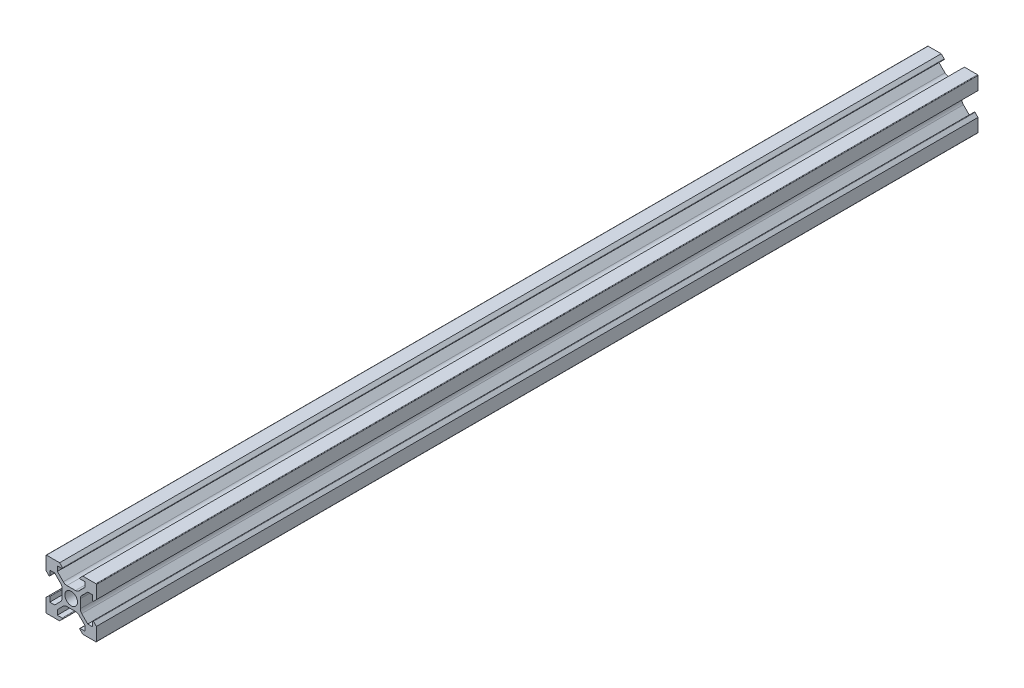
SolidWorks part; units mm, degrees
material "Liga 1350"
ref_plane "Plano frontal" through (0, 0, 0) normal (0, 0, 1) x (1, 0, 0)
ref_plane "Plano superior" through (0, 0, 0) normal (0, 1, 0) x (1, 0, 0)
ref_plane "Plano direito" through (0, 0, 0) normal (1, 0, 0) x (0, 0, -1)
sketch "Esboço1" plane through (0, 0, 0) normal (0, 0, 1) x (1, 0, 0)
  line L0 (0, 13.8681) -> (0, -15.879) construction
  line L1 (-4.6, -10) -> (-9.8, -10)
  line L2 (-3.4414, -8.8414) -> (-4.6, -10)
  line L3 (-4.1858, -3.1251) -> (-6.5607, -5.5)
  line L4 (-10, 9.8) -> (-10, 4.6)
  line L5 (-5.5, -8.5) -> (-3.5828, -8.5)
  line L6 (-5.5, -8.5) -> (-5.5, -6.5607)
  line L7 (-8.5, -5.5) -> (-8.5, -3.5828)
  line L8 (-21.5514, 0) -> (2.5, 0) construction
  line L9 (-3.1251, 4.1858) -> (-5.5, 6.5607)
  line L10 (-8.8414, -3.4414) -> (-10, -4.6)
  line L11 (-8.5, 5.5) -> (-6.5607, 5.5)
  line L12 (-8.8414, 3.4414) -> (-10, 4.6)
  line L13 (-8.5, -5.5) -> (-6.5607, -5.5)
  line L14 (-8.5, 5.5) -> (-8.5, 3.5828)
  line L15 (-3.1251, -4.1858) -> (-5.5, -6.5607)
  line L16 (-21.5514, 0) -> (20.6623, 0) construction
  line L17 (-8.5, 10) -> (-8.5, -10) construction
  line L18 (-10, -9.8) -> (-10, -4.6)
  line L19 (-21.5514, 5.5) -> (20.6623, 5.5) construction
  line L21 (-10, 10) -> (-10, -10) construction
  line L22 (3.6, 1.7109) -> (3.6, 0) construction
  line L23 (21.5514, 0) -> (-2.5, 0) construction
  line L24 (4.6, 10) -> (9.8, 10)
  line L25 (-5.5, 8.5) -> (-5.5, 6.5607)
  line L26 (3.4414, 8.8414) -> (4.6, 10)
  line L27 (-5.5, 8.5) -> (-3.5828, 8.5)
  line L28 (4.1858, 3.1251) -> (6.5607, 5.5)
  line L29 (5.5, 8.5) -> (3.5828, 8.5)
  line L30 (5.5, 8.5) -> (5.5, 6.5607)
  line L31 (-3.6, 1.7109) -> (-3.6, -1.7109)
  line L33 (10, -9.8) -> (10, -4.6)
  line L34 (-4.1858, 3.1251) -> (-6.5607, 5.5)
  line L35 (-3.4414, 8.8414) -> (-4.6, 10)
  line L36 (-4.6, 10) -> (-9.8, 10)
  line L37 (3.1251, -4.1858) -> (5.5, -6.5607)
  line L38 (8.5, 5.5) -> (8.5, 3.5828)
  line L39 (8.5, -5.5) -> (6.5607, -5.5)
  line L40 (8.8414, 3.4414) -> (10, 4.6)
  line L41 (8.5, 5.5) -> (6.5607, 5.5)
  line L42 (8.8414, -3.4414) -> (10, -4.6)
  line L43 (3.1251, 4.1858) -> (5.5, 6.5607)
  line L44 (8.5, -5.5) -> (8.5, -3.5828)
  line L45 (5.5, -8.5) -> (5.5, -6.5607)
  line L46 (5.5, -8.5) -> (3.5828, -8.5)
  line L47 (10, 9.8) -> (10, 4.6)
  line L48 (4.1858, -3.1251) -> (6.5607, -5.5)
  line L49 (3.4414, -8.8414) -> (4.6, -10)
  line L50 (4.6, -10) -> (9.8, -10)
  line L51 (-1.7109, 3.6) -> (1.7109, 3.6)
  line L52 (3.6, 1.7109) -> (3.6, -1.7109)
  line L53 (1.7109, -3.6) -> (-1.7109, -3.6)
  circle A0 centre (0, 0) radius 2.5
  arc A1 (-3.6, 1.7109) -> (-4.1858, 3.1251) centre (-5.6, 1.7109) ccw
  arc A2 (-8.5, 3.5828) -> (-8.8414, 3.4414) centre (-8.7, 3.5828) cw
  arc A3 (-9.8, 10) -> (-10, 9.8) centre (-9.8, 9.8) ccw
  arc A4 (-1.7109, 3.6) -> (-3.1251, 4.1858) centre (-1.7109, 5.6) cw
  arc A5 (-3.5828, 8.5) -> (-3.4414, 8.8414) centre (-3.5828, 8.7) ccw
  arc A6 (-3.5828, -8.5) -> (-3.4414, -8.8414) centre (-3.5828, -8.7) cw
  arc A7 (-1.7109, -3.6) -> (-3.1251, -4.1858) centre (-1.7109, -5.6) ccw
  arc A8 (-9.8, -10) -> (-10, -9.8) centre (-9.8, -9.8) cw
  arc A9 (-8.5, -3.5828) -> (-8.8414, -3.4414) centre (-8.7, -3.5828) ccw
  arc A10 (-3.6, -1.7109) -> (-4.1858, -3.1251) centre (-5.6, -1.7109) cw
  arc A11 (3.6, -1.7109) -> (4.1858, -3.1251) centre (5.6, -1.7109) ccw
  arc A12 (8.5, -3.5828) -> (8.8414, -3.4414) centre (8.7, -3.5828) cw
  arc A13 (9.8, -10) -> (10, -9.8) centre (9.8, -9.8) ccw
  arc A14 (1.7109, -3.6) -> (3.1251, -4.1858) centre (1.7109, -5.6) cw
  arc A15 (3.5828, -8.5) -> (3.4414, -8.8414) centre (3.5828, -8.7) ccw
  arc A16 (3.5828, 8.5) -> (3.4414, 8.8414) centre (3.5828, 8.7) cw
  arc A17 (1.7109, 3.6) -> (3.1251, 4.1858) centre (1.7109, 5.6) ccw
  arc A18 (9.8, 10) -> (10, 9.8) centre (9.8, 9.8) cw
  arc A19 (8.5, 3.5828) -> (8.8414, 3.4414) centre (8.7, 3.5828) ccw
  arc A20 (3.6, 1.7109) -> (4.1858, 3.1251) centre (5.6, 1.7109) cw
  point P0 (0, 0)
  point P45 (-3.6, 2.5393)
extrude "Ressalto-extrusão1" add sketch "Esboço1" along normal blind 350
